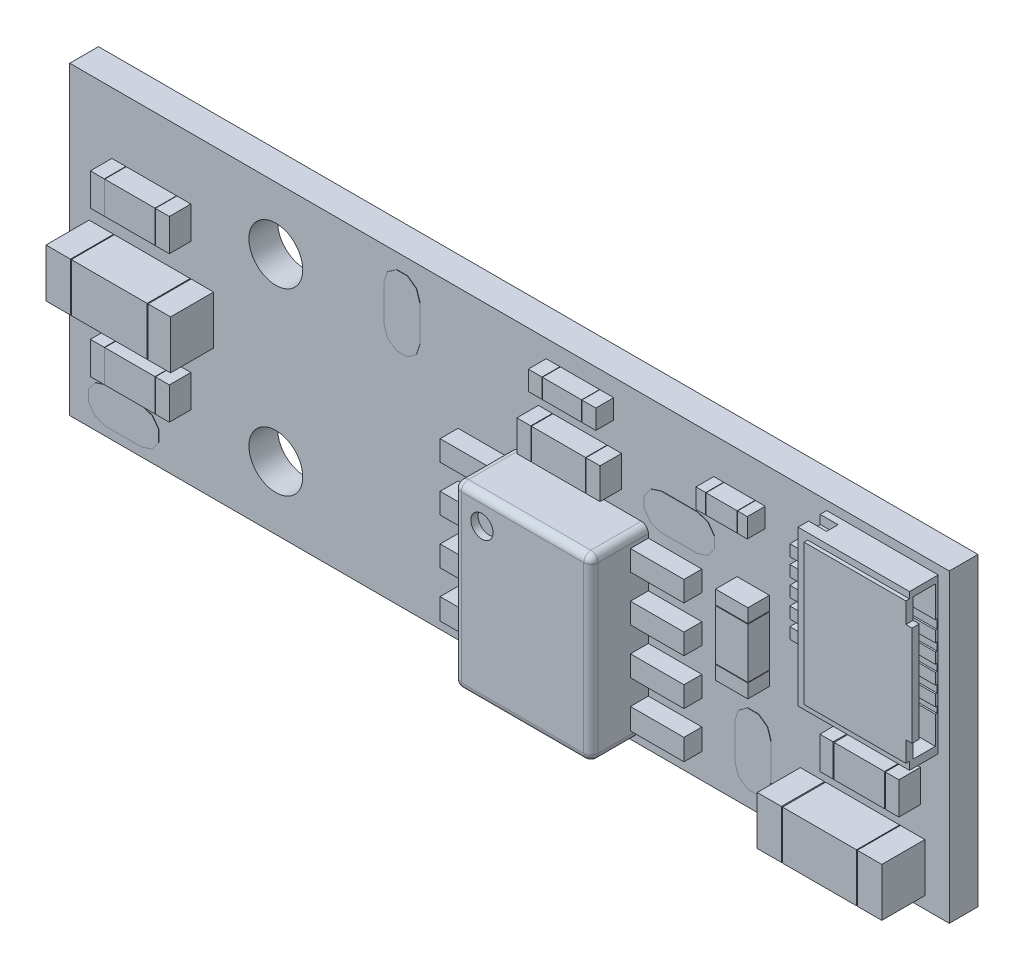
SolidWorks part; units mm, degrees
ref_plane "前视基准面" through (0, 0, 0) normal (0, 0, 1) x (1, 0, 0)
ref_plane "上视基准面" through (0, 0, 0) normal (0, 1, 0) x (1, 0, 0)
ref_plane "右视基准面" through (0, 0, 0) normal (1, 0, 0) x (0, 0, -1)
sketch "草图3" plane through (0, 0, 0) normal (0, 0, 1) x (1, 0, 0)
  line B0 (0, 8.5) -> (0, 0)
  line B1 (0.8695, 2.6826) -> (0.8695, 1.8826)
  line B2 (24.5, 8.5) -> (0, 8.5)
  line B3 (3.375, 5.891) -> (3.375, 6.791)
  line B4 (3.375, 6.791) -> (2.575, 6.791)
  line B5 (1.9793, 7.0564) -> (1.1793, 7.0564)
  line B6 (22.4108, 0.3313) -> (23.8205, 0.3313)
  line B7 (23.898, 0.1027) -> (22.4883, 0.1027)
  line B8 (0, 0) -> (24.5, 0)
  line B9 (22.4108, 1.6826) -> (22.4108, 0.3313)
  circle B10 centre (11.546, 5.452) radius 0.1499
  line B11 (9.1055, 6.1275) -> (8.8555, 6.3091)
  line B12 (21.7606, 1.6826) -> (20.3509, 1.6826)
  line B13 (21.0075, 6.2369) -> (20.3573, 6.2369)
  line B14 (20.3573, 5.9371) -> (21.0075, 5.9371)
  line B15 (19.489, 4.609) -> (19.489, 5.409)
  line B16 (18.589, 4.609) -> (19.489, 4.609)
  line B17 (17.8101, 3.7481) -> (17.8934, 3.547)
  line B18 (17.609, 3.8315) -> (17.8101, 3.7481)
  line B19 (16.2272, 3.8315) -> (17.609, 3.8315)
  line B20 (17.8101, 3.3458) -> (17.609, 3.2625)
  line B21 (17.8934, 3.547) -> (17.8101, 3.3458)
  arc B22 (18.3235, 3.2133) -> (18.6334, 2.9035) centre (18.6334, 3.2133) ccw
  line B23 (18.6345, 2.1819) -> (18.8845, 2.3635)
  line B24 (12.3999, 2.0758) -> (12.1988, 1.9925)
  line B25 (12.1988, 0.7225) -> (10.817, 0.7225)
  line B26 (12.1988, 1.9925) -> (10.817, 1.9925)
  line B27 (10.6158, 4.6158) -> (10.5325, 4.817)
  line B28 (12.1988, 4.5325) -> (10.817, 4.5325)
  line B29 (10.817, 3.8315) -> (12.1988, 3.8315)
  line B30 (10.817, 5.1015) -> (12.1988, 5.1015)
  line B31 (10.6158, 5.0182) -> (10.817, 5.1015)
  line B32 (3.665, 6.7408) -> (3.665, 5.9407)
  line B33 (2.575, 6.791) -> (2.575, 5.891)
  line B34 (1.9749, 5.891) -> (1.9749, 6.791)
  arc B35 (1.1793, 7.0564) -> (0.8694, 6.7466) centre (1.1793, 6.7466) ccw
  line B36 (1.9749, 6.791) -> (1.1749, 6.791)
  line B37 (2.575, 5.891) -> (3.375, 5.891)
  line B38 (2.5552, 5.631) -> (3.3552, 5.631)
  line B39 (2.6763, 5.2132) -> (4.086, 5.2132)
  line B40 (2.5988, 4.9846) -> (2.5988, 3.6334)
  line B41 (2.5552, 2.9866) -> (3.3552, 2.9866)
  line B42 (4.086, 3.4047) -> (2.6763, 3.4047)
  line B43 (1.9486, 3.6334) -> (1.9486, 4.9846)
  line B44 (1.9486, 4.9846) -> (0.5389, 4.9846)
  line B45 (2.5988, 3.6334) -> (4.0085, 3.6334)
  line B46 (2.5552, 1.567) -> (3.3552, 1.567)
  line B47 (1.9749, 1.827) -> (1.9749, 2.727)
  line B48 (1.9749, 2.727) -> (1.1749, 2.727)
  line B49 (2.575, 2.727) -> (2.575, 1.827)
  line B50 (2.575, 1.827) -> (3.375, 1.827)
  line B51 (17.8934, 4.817) -> (17.8101, 4.6158)
  line B52 (18.589, 5.409) -> (18.589, 4.609)
  circle B53 centre (19.039, 4.944) radius 0.305
  line B54 (20.3573, 5.2361) -> (20.3573, 4.9364)
  line B55 (20.3573, 5.4368) -> (21.0075, 5.4368)
  line B56 (19.749, 4.5893) -> (19.749, 5.3892)
  circle B57 centre (22.087, 6.3267) radius 0.305
  line B58 (20.3573, 6.9379) -> (21.0075, 6.9379)
  line B59 (19.6022, 7.7286) -> (19.6022, 6.7314)
  line B60 (19.3736, 6.96) -> (19.3736, 7.5)
  line B61 (18.808, 7.5) -> (18.808, 6.96)
  line B62 (18.508, 6.96) -> (18.508, 7.5)
  line B63 (17.9423, 6.96) -> (18.508, 6.96)
  line B64 (17.9423, 7.5) -> (17.9423, 6.96)
  line B65 (15.5973, 7.0014) -> (14.6397, 7.0014)
  line B66 (12.8287, 5.6806) -> (12.8287, 7.0014)
  line B67 (13.8625, 6.7728) -> (13.0547, 6.7728)
  line B68 (14.5635, 6.7728) -> (14.5635, 5.9092)
  line B69 (14.5635, 5.9092) -> (15.3712, 5.9092)
  line B70 (14.4392, 7.2394) -> (15.2293, 7.2394)
  line B71 (14.363, 7.468) -> (15.1531, 7.468)
  line B72 (14.363, 8.008) -> (14.363, 7.468)
  line B73 (14.0629, 7.468) -> (14.0629, 8.008)
  line B74 (14.0629, 8.008) -> (13.2728, 8.008)
  line B75 (15.3712, 6.7728) -> (14.5635, 6.7728)
  line B76 (16.0315, 5.8055) -> (16.0315, 6.1145)
  circle B77 centre (19.547, 6.214) radius 0.305
  line B78 (21.0075, 5.7365) -> (20.3573, 5.7365)
  line B79 (21.0075, 5.9371) -> (21.0075, 6.2369)
  line B80 (18.508, 7.5) -> (17.9423, 7.5)
  line B81 (18.808, 6.96) -> (19.3736, 6.96)
  line B82 (22.7918, 3.9369) -> (24.1914, 3.9369)
  line B83 (23.985, 3.3118) -> (23.985, 2.5117)
  line B84 (23.695, 2.462) -> (23.695, 3.362)
  line B85 (22.895, 2.462) -> (23.695, 2.462)
  line B86 (23.8205, 1.6826) -> (22.4108, 1.6826)
  line B87 (22.295, 2.462) -> (22.295, 3.362)
  line B88 (22.295, 3.362) -> (21.495, 3.362)
  line B89 (20.1236, 1.7588) -> (20.1236, 0.2551)
  line B90 (19.539, 1.888) -> (19.539, 0.888)
  line B91 (17.609, 1.9925) -> (16.2272, 1.9925)
  line B92 (17.609, 3.2625) -> (16.2272, 3.2625)
  line B93 (18.589, 3.209) -> (19.489, 3.209)
  line B94 (19.489, 3.209) -> (19.489, 4.009)
  arc B95 (19.749, 5.3892) -> (19.4392, 5.699) centre (19.4392, 5.3892) ccw
  line B96 (19.489, 5.409) -> (18.589, 5.409)
  line B97 (19.489, 4.009) -> (18.589, 4.009)
  line B98 (18.3294, 4.5893) -> (18.3294, 5.3892)
  line B99 (17.609, 4.5325) -> (16.2272, 4.5325)
  line B100 (20.3509, 0.3313) -> (21.7606, 0.3313)
  line B101 (20.276, 0.1027) -> (21.6857, 0.1027)
  line B102 (16.2272, 5.1015) -> (17.609, 5.1015)
  line B103 (15.5973, 5.6806) -> (15.5973, 7.0014)
  line B104 (13.1967, 8.2366) -> (13.9868, 8.2366)
  line B105 (17.7137, 6.7314) -> (18.4318, 6.7314)
  line B106 (20.3573, 6.2369) -> (20.3573, 5.9371)
  line B107 (23.9869, 7.5577) -> (23.9869, 4.6163)
  line B108 (24.3882, 7.8472) -> (24.3882, 4.3217)
  line B109 (17.7137, 7.7286) -> (17.7137, 6.7314)
  line B110 (15.3817, 7.3918) -> (15.3817, 8.0842)
  line B111 (19.6022, 6.7314) -> (18.8842, 6.7314)
  line B112 (18.4318, 7.7286) -> (17.7137, 7.7286)
  line B113 (12.1988, 3.8315) -> (12.3999, 3.7481)
  line B114 (18.3235, 4.0134) -> (18.3235, 3.2134)
  line B115 (21.7606, 0.3313) -> (21.7606, 1.6826)
  line B116 (17.609, 1.2915) -> (17.8101, 1.2081)
  circle B117 centre (14.213, 1.769) radius 0.305
  line B118 (4.2384, 5.0608) -> (4.2384, 3.5572)
  line B119 (0.3115, 5.0608) -> (0.3115, 3.5572)
  line B120 (3.665, 2.6768) -> (3.665, 1.8767)
  circle B121 centre (13.324, 1.007) radius 0.305
  line B122 (13.2728, 7.468) -> (14.0629, 7.468)
  line B123 (12.3999, 1.2081) -> (12.4832, 1.007)
  line B124 (15.7141, 0.4126) -> (12.7118, 0.4126)
  line B125 (12.7118, 0.4126) -> (12.308, 0.4126)
  line B126 (10.817, 1.2915) -> (12.1988, 1.2915)
  line B127 (12.1988, 3.2625) -> (10.817, 3.2625)
  line B128 (12.3999, 3.7481) -> (12.4832, 3.547)
  line B129 (4.0085, 4.9846) -> (2.5988, 4.9846)
  line B130 (8.8555, 6.3091) -> (8.76, 6.603)
  line B131 (12.3999, 2.4781) -> (12.4832, 2.277)
  line B132 (13.2728, 8.008) -> (13.2728, 7.468)
  line B133 (13.0547, 6.7728) -> (13.0547, 5.9092)
  line B134 (13.7863, 5.6806) -> (12.8287, 5.6806)
  line B135 (12.3999, 3.3458) -> (12.1988, 3.2625)
  line B136 (12.7118, 5.4114) -> (13.4865, 5.4114)
  circle B137 centre (3.291, 4.309) radius 0.305
  line B138 (1.1749, 5.891) -> (1.9749, 5.891)
  arc B139 (0.8694, 5.9466) -> (1.1793, 5.6368) centre (1.1793, 5.9466) ccw
  line B140 (1.8736, 5.2132) -> (0.4639, 5.2132)
  line B141 (3.375, 1.827) -> (3.375, 2.727)
  line B142 (1.1749, 1.827) -> (1.9749, 1.827)
  line B143 (1.1749, 2.727) -> (1.1749, 1.827)
  arc B144 (0.8694, 1.8826) -> (1.1793, 1.5728) centre (1.1793, 1.8826) ccw
  line B145 (10.6158, 1.2081) -> (10.817, 1.2915)
  line B146 (16.026, 3.3458) -> (15.9427, 3.547)
  line B147 (16.026, 3.7481) -> (16.2272, 3.8315)
  arc B148 (13.4864, 5.412) -> (14.9393, 5.4071) centre (14.213, 5.4518) ccw
  line B149 (14.6397, 5.6806) -> (15.5973, 5.6806)
  line B150 (15.3712, 5.9092) -> (15.3712, 6.7728)
  line B151 (12.7118, 5.4114) -> (12.308, 5.4114)
  line B152 (13.8625, 5.9092) -> (13.8625, 6.7728)
  line B153 (13.0547, 5.9092) -> (13.8625, 5.9092)
  line B154 (16.026, 4.6158) -> (15.9427, 4.817)
  line B155 (21.6857, 1.9112) -> (20.276, 1.9112)
  line B156 (22.8753, 2.202) -> (23.6752, 2.202)
  line B157 (21.495, 2.462) -> (22.295, 2.462)
  line B158 (22.895, 3.362) -> (22.895, 2.462)
  line B159 (16.507, 5.46) -> (16.2131, 5.5555)
  line B160 (18.6392, 5.699) -> (19.4392, 5.699)
  line B161 (17.9825, 5.8055) -> (17.8009, 5.5555)
  line B162 (16.026, 5.0182) -> (16.2272, 5.1015)
  line B163 (10.817, 3.8315) -> (12.1988, 3.8315)
  line B164 (16.2272, 1.2915) -> (17.609, 1.2915)
  line B165 (16.2272, 1.2915) -> (17.609, 1.2915)
  line B166 (17.609, 1.2915) -> (17.8101, 1.2081)
  line B167 (14.363, 7.468) -> (15.1531, 7.468)
  line B168 (13.0547, 6.7728) -> (13.0547, 5.9092)
  line B169 (1.1749, 5.891) -> (1.9749, 5.891)
  line B170 (15.9427, 2.277) -> (16.026, 2.4781)
  line B171 (0.5389, 3.6334) -> (1.9486, 3.6334)
  line B172 (0.5389, 4.9846) -> (0.5389, 3.6334)
  line B173 (0.4639, 3.4047) -> (1.8736, 3.4047)
  line B174 (1.9793, 2.9924) -> (1.1793, 2.9924)
  line B175 (16.2272, 2.5615) -> (17.609, 2.5615)
  line B176 (2.5552, 7.0506) -> (3.3552, 7.0506)
  line B177 (2.4885, 0.5985) -> (2.3068, 0.3485)
  line B178 (3.375, 2.727) -> (2.575, 2.727)
  line B179 (0.5374, 0.9075) -> (0.7191, 1.1575)
  line B180 (22.4883, 1.9112) -> (23.898, 1.9112)
  line B181 (23.695, 3.362) -> (22.895, 3.362)
  line B182 (17.507, 5.46) -> (16.507, 5.46)
  line B183 (12.8287, 7.0014) -> (13.7863, 7.0014)
  line B184 (12.4832, 4.817) -> (12.3999, 4.6158)
  line B185 (19.7432, 4.0134) -> (19.7432, 3.2134)
  line B186 (19.489, 3.209) -> (19.489, 4.009)
  line B187 (18.589, 4.609) -> (19.489, 4.609)
  line B188 (14.5635, 5.9092) -> (15.3712, 5.9092)
  line B189 (14.5635, 6.7728) -> (14.5635, 5.9092)
  line B190 (18.589, 4.009) -> (18.589, 3.209)
  line B191 (17.8101, 2.0758) -> (17.609, 1.9925)
  arc B192 (19.4334, 2.9035) -> (19.7432, 3.2133) centre (19.4334, 3.2133) ccw
  line B193 (18.6334, 2.9035) -> (19.4334, 2.9035)
  line B194 (10.817, 2.5615) -> (12.1988, 2.5615)
  line B195 (17.8009, 6.3645) -> (17.9825, 6.1145)
  line B196 (17.507, 6.46) -> (17.8009, 6.3645)
  line B197 (21.0075, 5.2361) -> (20.3573, 5.2361)
  line B198 (21.0075, 4.9364) -> (21.0075, 5.2361)
  line B199 (21.0862, 3.9229) -> (22.6128, 3.9229)
  line B200 (22.2994, 2.2078) -> (21.4994, 2.2078)
  line B201 (23.8205, 0.3313) -> (23.8205, 1.6826)
  line B202 (24.5, 0) -> (24.5, 8.5)
  line B203 (1.1749, 6.791) -> (1.1749, 5.891)
  line B204 (1.1749, 6.791) -> (1.1749, 5.891)
  arc B205 (21.1895, 2.5176) -> (21.4993, 2.2078) centre (21.4993, 2.5176) ccw
  line B206 (21.1895, 3.3176) -> (21.1895, 2.5176)
  arc B207 (21.4993, 3.6274) -> (21.1895, 3.3176) centre (21.4993, 3.3176) ccw
  line B208 (24.0504, 1.7588) -> (24.0504, 0.2551)
  line B209 (18.6345, 0.5941) -> (18.539, 0.888)
  line B210 (17.609, 2.5615) -> (17.8101, 2.4781)
  line B211 (21.495, 3.362) -> (21.495, 2.462)
  line B212 (15.2293, 8.2366) -> (14.4392, 8.2366)
  line B213 (15.1531, 7.468) -> (15.1531, 8.008)
  line B214 (15.1531, 8.008) -> (14.363, 8.008)
  line B215 (19.3736, 7.5) -> (18.808, 7.5)
  line B216 (10.6158, 2.0758) -> (10.5325, 2.277)
  line B217 (16.507, 5.46) -> (16.2131, 5.5555)
  line B218 (16.507, 6.46) -> (17.507, 6.46)
  line B219 (17.8934, 2.277) -> (17.8101, 2.0758)
  line B220 (18.539, 1.888) -> (18.6345, 2.1819)
  line B221 (17.8101, 2.4781) -> (17.8934, 2.277)
  line B222 (12.3999, 5.0182) -> (12.4832, 4.817)
  line B223 (12.1988, 5.1015) -> (12.3999, 5.0182)
  line B224 (9.6645, 6.3091) -> (9.4145, 6.1275)
  line B225 (9.76, 6.603) -> (9.6645, 6.3091)
  line B226 (9.76, 7.603) -> (9.76, 6.603)
  line B227 (10.5325, 4.817) -> (10.6158, 5.0182)
  line B228 (10.817, 4.5325) -> (10.6158, 4.6158)
  line B229 (16.026, 0.8058) -> (15.9427, 1.007)
  line B230 (16.2272, 0.7225) -> (16.026, 0.8058)
  line B231 (12.4832, 3.547) -> (12.3999, 3.3458)
  line B232 (10.5325, 1.007) -> (10.6158, 1.2081)
  line B233 (16.2272, 1.9925) -> (16.026, 2.0758)
  line B234 (12.3999, 4.6158) -> (12.1988, 4.5325)
  line B235 (12.3999, 0.8058) -> (12.1988, 0.7225)
  line B236 (18.539, 0.888) -> (18.539, 1.888)
  line B237 (16.026, 2.4781) -> (16.2272, 2.5615)
  line B238 (16.2272, 3.2625) -> (16.026, 3.3458)
  line B239 (17.609, 5.1015) -> (17.8101, 5.0182)
  line B240 (16.2272, 4.5325) -> (16.026, 4.6158)
  line B241 (13.9868, 7.2394) -> (13.1967, 7.2394)
  line B242 (17.609, 0.7225) -> (16.2272, 0.7225)
  line B243 (15.9427, 3.547) -> (16.026, 3.7481)
  line B244 (13.0443, 7.3918) -> (13.0443, 8.0842)
  line B245 (15.7141, 5.4114) -> (14.9394, 5.4114)
  line B246 (24.1914, 4.4373) -> (22.7918, 4.4373)
  line B247 (12.4832, 2.277) -> (12.3999, 2.0758)
  circle B248 centre (22.087, 7.23) radius 0.305
  line B249 (21.0862, 8.2511) -> (22.6128, 8.2511)
  line B250 (21.0862, 8.2511) -> (21.0862, 7.3976)
  line B251 (22.7918, 7.7367) -> (24.1914, 7.7367)
  line B252 (22.7918, 7.7367) -> (24.1914, 7.7367)
  line B253 (21.0075, 7.2376) -> (20.3573, 7.2376)
  line B254 (21.0075, 6.7372) -> (20.3573, 6.7372)
  line B255 (20.3573, 6.4375) -> (21.0075, 6.4375)
  line B256 (20.3573, 5.7365) -> (20.3573, 5.4368)
  line B257 (20.3573, 4.9364) -> (21.0075, 4.9364)
  line B258 (21.0862, 3.9229) -> (21.0862, 4.7764)
  line B259 (24.1914, 8.2371) -> (22.7918, 8.2371)
  line B260 (22.7918, 8.2371) -> (22.7918, 7.7367)
  arc B261 (18.6392, 5.699) -> (18.3294, 5.3892) centre (18.6392, 5.3892) ccw
  line B262 (17.8009, 5.5555) -> (17.507, 5.46)
  line B263 (19.489, 4.009) -> (18.589, 4.009)
  line B264 (19.4435, 2.1819) -> (19.539, 1.888)
  line B265 (19.4435, 2.1819) -> (19.539, 1.888)
  line B266 (22.4108, 1.6826) -> (22.4108, 0.3313)
  line B267 (22.4108, 0.3313) -> (23.8205, 0.3313)
  line B268 (20.3509, 1.6826) -> (20.3509, 0.3313)
  line B269 (20.3509, 1.6826) -> (20.3509, 0.3313)
  line B270 (21.0075, 7.2376) -> (20.3573, 7.2376)
  line B271 (20.3573, 6.4375) -> (21.0075, 6.4375)
  line B272 (22.7918, 8.2371) -> (22.7918, 7.7367)
  line B273 (21.0075, 6.2369) -> (20.3573, 6.2369)
  line B274 (21.0075, 4.9364) -> (21.0075, 5.2361)
  line B275 (20.3573, 5.9371) -> (21.0075, 5.9371)
  line B276 (19.1935, 2.3635) -> (19.4435, 2.1819)
  line B277 (19.1935, 2.3635) -> (19.4435, 2.1819)
  line B278 (21.0075, 5.2361) -> (20.3573, 5.2361)
  line B279 (21.7606, 1.6826) -> (20.3509, 1.6826)
  line B280 (20.3509, 0.3313) -> (21.7606, 0.3313)
  line B281 (10.6158, 3.3458) -> (10.5325, 3.547)
  line B282 (10.817, 3.2625) -> (10.6158, 3.3458)
  line B283 (0.7191, 1.1575) -> (1.013, 1.253)
  line B284 (2.3068, 1.1575) -> (2.4885, 0.9075)
  line B285 (2.4885, 0.9075) -> (2.4885, 0.5985)
  arc B286 (0.4638, 5.2126) -> (0.3114, 5.0602) centre (0.4638, 5.0602) ccw
  line B287 (8.76, 7.603) -> (8.8555, 7.8969)
  line B288 (2.013, 0.253) -> (1.013, 0.253)
  line B289 (8.76, 6.603) -> (8.76, 7.603)
  line B290 (9.6645, 7.8969) -> (9.76, 7.603)
  line B291 (9.4145, 8.0785) -> (9.6645, 7.8969)
  line B292 (9.1055, 8.0785) -> (9.4145, 8.0785)
  line B293 (8.8555, 7.8969) -> (9.1055, 8.0785)
  line B294 (9.4145, 6.1275) -> (9.1055, 6.1275)
  line B295 (1.9793, 1.5728) -> (1.1793, 1.5728)
  line B296 (2.013, 1.253) -> (2.3068, 1.1575)
  line B297 (0.5374, 0.5985) -> (0.5374, 0.9075)
  line B298 (0.7191, 0.3485) -> (0.5374, 0.5985)
  line B299 (1.013, 0.253) -> (0.7191, 0.3485)
  line B300 (2.3068, 0.3485) -> (2.013, 0.253)
  line B301 (1.013, 1.253) -> (2.013, 1.253)
  line B302 (10.5325, 2.277) -> (10.6158, 2.4781)
  line B303 (12.1988, 2.5615) -> (12.3999, 2.4781)
  arc B304 (1.1793, 2.9924) -> (0.8694, 2.6826) centre (1.1793, 2.6826) ccw
sketch_block_instance "DXF_PCB3_2023-05-06 (4)-1"
sketch_block "DXF_PCB3_2023-05-06 (4)"
sketch "草图4" plane through (0, 0, 0) normal (0, 0, 1) x (1, 0, 0)
  line L1 (24.5, 0) -> (0, 0)
  line L2 (24.5, 0) -> (24.5, 8.5)
  line L3 (24.5, 8.5) -> (0, 8.5)
  line L4 (0, 0) -> (0, 8.5)
extrude "凸台-拉伸1" add sketch "草图4" along normal blind 0.8
sketch "草图5" plane through (0, 0, 0.8) normal (0, 0, 1) x (1, 0, 0)
  line L0 (1.9749, 6.791) -> (1.1749, 6.791) construction
  line L1 (1.5749, 6.791) -> (2.975, 6.791)
  line L2 (1.5749, 6.791) -> (1.5749, 5.891)
  line L3 (1.5749, 5.891) -> (2.975, 5.891)
  line L4 (2.975, 6.791) -> (2.975, 5.891)
  line L5 (2.575, 5.891) -> (3.375, 5.891) construction
  line L12 (1.9749, 2.727) -> (1.1749, 2.727) construction
  line L13 (1.5749, 2.727) -> (2.975, 2.727)
  line L14 (1.5749, 2.727) -> (1.5749, 1.827)
  line L15 (1.5749, 1.827) -> (2.975, 1.827)
  line L16 (2.975, 2.727) -> (2.975, 1.827)
  line L17 (2.575, 1.827) -> (3.375, 1.827) construction
  line L18 (13.8625, 6.7728) -> (13.0547, 6.7728) construction
  line L19 (13.4586, 6.7728) -> (14.9674, 6.7728)
  line L20 (13.4586, 6.7728) -> (13.4586, 5.9092)
  line L21 (13.4586, 5.9092) -> (14.9674, 5.9092)
  line L22 (14.9674, 6.7728) -> (14.9674, 5.9092)
  line L23 (14.5635, 5.9092) -> (15.3712, 5.9092) construction
  line L36 (22.295, 3.362) -> (21.495, 3.362) construction
  line L37 (21.895, 3.362) -> (23.295, 3.362)
  line L38 (21.895, 3.362) -> (21.895, 2.462)
  line L39 (21.895, 2.462) -> (23.295, 2.462)
  line L40 (23.295, 3.362) -> (23.295, 2.462)
  line L41 (22.895, 2.462) -> (23.695, 2.462) construction
  line L48 (18.589, 5.409) -> (18.589, 4.609) construction
  line L49 (18.589, 5.009) -> (19.489, 5.009)
  line L50 (18.589, 5.009) -> (18.589, 3.609)
  line L51 (18.589, 3.609) -> (19.489, 3.609)
  line L52 (19.489, 5.009) -> (19.489, 3.609)
  line L53 (19.489, 3.209) -> (19.489, 4.009) construction
extrude "凸台-拉伸2" add sketch "草图5" along normal blind 0.6
sketch "草图7" plane through (0, 0, 0.8) normal (0, 0, 1) x (1, 0, 0)
  line L0 (3.375, 6.791) -> (2.575, 6.791) construction
  line L1 (3.375, 5.891) -> (2.9856, 5.891)
  line L2 (3.375, 5.891) -> (3.375, 6.791)
  line L3 (3.375, 6.791) -> (2.9856, 6.791)
  line L4 (2.9856, 5.891) -> (2.9856, 6.791)
  line L5 (1.1749, 5.891) -> (1.9749, 5.891) construction
  line L6 (1.1749, 6.791) -> (1.5619, 6.791)
  line L7 (1.1749, 6.791) -> (1.1749, 5.891)
  line L8 (1.1749, 5.891) -> (1.5619, 5.891)
  line L9 (1.5619, 6.791) -> (1.5619, 5.891)
  line L10 (2.575, 1.827) -> (3.375, 1.827) construction
  line L11 (3.375, 2.727) -> (2.9856, 2.727)
  line L12 (3.375, 2.727) -> (3.375, 1.827)
  line L13 (3.375, 1.827) -> (2.9856, 1.827)
  line L14 (2.9856, 2.727) -> (2.9856, 1.827)
  line L15 (1.1749, 1.827) -> (1.9749, 1.827) construction
  line L16 (1.1749, 2.727) -> (1.5619, 2.727)
  line L17 (1.1749, 2.727) -> (1.1749, 1.827)
  line L18 (1.1749, 1.827) -> (1.5619, 1.827)
  line L19 (1.5619, 2.727) -> (1.5619, 1.827)
  line L20 (23.695, 3.362) -> (22.895, 3.362) construction
  line L21 (23.695, 2.462) -> (23.3206, 2.462)
  line L22 (23.695, 2.462) -> (23.695, 3.362)
  line L23 (23.695, 3.362) -> (23.3206, 3.362)
  line L24 (23.3206, 2.462) -> (23.3206, 3.362)
  line L25 (21.495, 2.462) -> (22.295, 2.462) construction
  line L26 (21.495, 3.362) -> (21.8643, 3.362)
  line L27 (21.495, 3.362) -> (21.495, 2.462)
  line L28 (21.495, 2.462) -> (21.8643, 2.462)
  line L29 (21.8643, 3.362) -> (21.8643, 2.462)
  line L30 (13.0547, 5.9092) -> (13.8625, 5.9092) construction
  line L31 (13.0547, 6.7728) -> (13.4422, 6.7728)
  line L32 (13.0547, 6.7728) -> (13.0547, 5.9092)
  line L33 (13.0547, 5.9092) -> (13.4422, 5.9092)
  line L34 (13.4422, 6.7728) -> (13.4422, 5.9092)
  line L35 (14.5635, 5.9092) -> (15.3712, 5.9092) construction
  line L36 (15.3712, 6.7728) -> (14.979, 6.7728)
  line L37 (15.3712, 6.7728) -> (15.3712, 5.9092)
  line L38 (15.3712, 5.9092) -> (14.979, 5.9092)
  line L39 (14.979, 6.7728) -> (14.979, 5.9092)
  line L40 (19.489, 3.209) -> (19.489, 4.009) construction
  line L41 (18.589, 3.209) -> (19.489, 3.209)
  line L42 (18.589, 3.209) -> (18.589, 3.593)
  line L43 (18.589, 3.593) -> (19.489, 3.593)
  line L44 (19.489, 3.209) -> (19.489, 3.593)
  line L45 (19.489, 4.609) -> (19.489, 5.409) construction
  line L46 (18.589, 5.409) -> (19.489, 5.409)
  line L47 (18.589, 5.409) -> (18.589, 5.0285)
  line L48 (18.589, 5.0285) -> (19.489, 5.0285)
  line L49 (19.489, 5.409) -> (19.489, 5.0285)
extrude "凸台-拉伸4" add sketch "草图7" along normal blind 0.6
sketch "草图8" plane through (0, 0, 0.8) normal (0, 0, 1) x (1, 0, 0)
  line L0 (1.9486, 4.9846) -> (0.5389, 4.9846) construction
  line L1 (1.2437, 4.9846) -> (3.3552, 4.9846)
  line L2 (1.2437, 4.9846) -> (1.2437, 3.6334)
  line L3 (1.2437, 3.6334) -> (3.3552, 3.6334)
  line L4 (3.3552, 4.9846) -> (3.3552, 3.6334)
  line L5 (2.5988, 3.6334) -> (4.0085, 3.6334) construction
  line L6 (21.7606, 1.6826) -> (20.3509, 1.6826) construction
  line L7 (21.0558, 1.6826) -> (23.1157, 1.6826)
  line L8 (21.0558, 1.6826) -> (21.0558, 0.3313)
  line L9 (21.0558, 0.3313) -> (23.1157, 0.3313)
  line L10 (23.1157, 1.6826) -> (23.1157, 0.3313)
  line L11 (22.4108, 0.3313) -> (23.8205, 0.3313) construction
extrude "凸台-拉伸5" add sketch "草图8" along normal blind 1.2
sketch "草图9" plane through (0, 0, 0.8) normal (0, 0, 1) x (1, 0, 0)
  line L0 (0.5389, 3.6334) -> (1.9486, 3.6334) construction
  line L1 (0.5389, 4.9846) -> (1.221, 4.9846)
  line L2 (0.5389, 4.9846) -> (0.5389, 3.6334)
  line L3 (0.5389, 3.6334) -> (1.221, 3.6334)
  line L4 (1.221, 4.9846) -> (1.221, 3.6334)
  line L5 (2.5988, 3.6334) -> (4.0085, 3.6334) construction
  line L6 (4.0085, 4.9846) -> (3.382, 4.9846)
  line L7 (4.0085, 4.9846) -> (4.0085, 3.6334)
  line L8 (4.0085, 3.6334) -> (3.382, 3.6334)
  line L9 (3.382, 4.9846) -> (3.382, 3.6334)
  line L10 (20.3509, 0.3313) -> (21.7606, 0.3313) construction
  line L11 (20.3509, 1.6826) -> (21.0239, 1.6826)
  line L12 (20.3509, 1.6826) -> (20.3509, 0.3313)
  line L13 (20.3509, 0.3313) -> (21.0239, 0.3313)
  line L14 (21.0239, 1.6826) -> (21.0239, 0.3313)
  line L15 (22.4108, 0.3313) -> (23.8205, 0.3313) construction
  line L16 (23.8205, 1.6826) -> (23.1383, 1.6826)
  line L17 (23.8205, 1.6826) -> (23.8205, 0.3313)
  line L18 (23.8205, 0.3313) -> (23.1383, 0.3313)
  line L19 (23.1383, 1.6826) -> (23.1383, 0.3313)
extrude "凸台-拉伸6" add sketch "草图9" along normal blind 1.2
sketch "草图10" plane through (0, 0, 0.8) normal (0, 0, 1) x (1, 0, 0)
  line L0 (14.0629, 8.008) -> (13.2728, 8.008) construction
  line L1 (13.6679, 8.008) -> (14.7581, 8.008)
  line L2 (13.6679, 8.008) -> (13.6679, 7.468)
  line L3 (13.6679, 7.468) -> (14.7581, 7.468)
  line L4 (14.7581, 8.008) -> (14.7581, 7.468)
  line L5 (14.363, 7.468) -> (15.1531, 7.468) construction
  line L6 (18.508, 7.5) -> (17.9423, 7.5) construction
  line L7 (18.2252, 7.5) -> (19.0908, 7.5)
  line L8 (18.2252, 7.5) -> (18.2252, 6.96)
  line L9 (18.2252, 6.96) -> (19.0908, 6.96)
  line L10 (19.0908, 7.5) -> (19.0908, 6.96)
  line L11 (18.808, 6.96) -> (19.3736, 6.96) construction
extrude "凸台-拉伸7" add sketch "草图10" along normal blind 0.5
sketch "草图11" plane through (0, 0, 0.8) normal (0, 0, 1) x (1, 0, 0)
  line L0 (13.2728, 7.468) -> (14.0629, 7.468) construction
  line L1 (13.2728, 8.008) -> (13.6561, 8.008)
  line L2 (13.2728, 8.008) -> (13.2728, 7.468)
  line L3 (13.2728, 7.468) -> (13.6561, 7.468)
  line L4 (13.6561, 8.008) -> (13.6561, 7.468)
  line L5 (14.363, 7.468) -> (15.1531, 7.468) construction
  line L6 (15.1531, 8.008) -> (14.7661, 8.008)
  line L7 (15.1531, 8.008) -> (15.1531, 7.468)
  line L8 (15.1531, 7.468) -> (14.7661, 7.468)
  line L9 (14.7661, 8.008) -> (14.7661, 7.468)
  line L10 (17.9423, 6.96) -> (18.508, 6.96) construction
  line L11 (17.9423, 7.5) -> (18.214, 7.5)
  line L12 (17.9423, 7.5) -> (17.9423, 6.96)
  line L13 (17.9423, 6.96) -> (18.214, 6.96)
  line L14 (18.214, 7.5) -> (18.214, 6.96)
  line L15 (18.808, 6.96) -> (19.3736, 6.96) construction
  line L16 (19.3736, 7.5) -> (19.1014, 7.5)
  line L17 (19.3736, 7.5) -> (19.3736, 6.96)
  line L18 (19.3736, 6.96) -> (19.1014, 6.96)
  line L19 (19.1014, 7.5) -> (19.1014, 6.96)
extrude "凸台-拉伸8" add sketch "草图11" along normal blind 0.5
sketch "草图12" plane through (0, 0, 0.8) normal (0, 0, 1) x (1, 0, 0)
  line L1 (12.308, 5.4114) -> (16.118, 5.4114)
  line L2 (12.308, 5.4114) -> (12.308, 0.4126)
  line L3 (12.308, 0.4126) -> (16.118, 0.4126)
  line L4 (16.118, 5.4114) -> (16.118, 0.4126)
extrude "凸台-拉伸9" add sketch "草图12" along normal blind 1.6
sketch "草图13" plane through (0, 0, 0.8) normal (0, 0, 1) x (1, 0, 0)
  line L0 (12.308, 5.4114) -> (12.308, 0.4126) construction
  line L1 (10.817, 5.1015) -> (12.308, 5.1015)
  line L2 (10.817, 5.1015) -> (10.817, 4.5336)
  line L3 (10.817, 4.5336) -> (12.308, 4.5336)
  line L4 (12.308, 5.1015) -> (12.308, 4.5336)
  line L5 (16.118, 0.4126) -> (16.118, 5.4114) construction
  line L6 (10.817, 3.8315) -> (12.308, 3.8315)
  line L7 (10.817, 3.8315) -> (10.817, 3.2596)
  line L8 (10.817, 3.2596) -> (12.308, 3.2596)
  line L9 (12.308, 3.8315) -> (12.308, 3.2596)
  line L10 (10.817, 2.5615) -> (12.308, 2.5615)
  line L11 (10.817, 2.5615) -> (10.817, 1.9853)
  line L12 (10.817, 1.9853) -> (12.308, 1.9853)
  line L13 (12.308, 2.5615) -> (12.308, 1.9853)
  line L14 (10.817, 1.2915) -> (12.308, 1.2915)
  line L15 (10.817, 1.2915) -> (10.817, 0.7015)
  line L16 (10.817, 0.7015) -> (12.308, 0.7015)
  line L17 (12.308, 1.2915) -> (12.308, 0.7015)
  line L18 (17.609, 1.2915) -> (16.118, 1.2915)
  line L19 (17.609, 1.2915) -> (17.609, 0.7015)
  line L20 (17.609, 0.7015) -> (16.118, 0.7015)
  line L21 (16.118, 1.2915) -> (16.118, 0.7015)
  line L22 (16.118, 0.4126) -> (16.118, 5.4114) construction
  line L23 (17.609, 2.5615) -> (16.118, 2.5615)
  line L24 (17.609, 2.5615) -> (17.609, 1.9853)
  line L25 (17.609, 1.9853) -> (16.118, 1.9853)
  line L26 (16.118, 2.5615) -> (16.118, 1.9853)
  line L27 (17.609, 3.8315) -> (16.118, 3.8315)
  line L28 (17.609, 3.8315) -> (17.609, 3.2596)
  line L29 (17.609, 3.2596) -> (16.118, 3.2596)
  line L30 (16.118, 3.8315) -> (16.118, 3.2596)
  line L32 (17.609, 5.1015) -> (16.118, 5.1015)
  line L33 (17.609, 5.1015) -> (17.609, 4.5336)
  line L34 (17.609, 4.5336) -> (16.118, 4.5336)
  line L35 (16.118, 5.1015) -> (16.118, 4.5336)
extrude "凸台-拉伸10" add sketch "草图13" along normal blind 0.5
sketch "草图14" plane through (0, 0, 2.4) normal (0, 0, 1) x (1, 0, 0)
  circle A0 centre (13.0829, 4.6684) radius 0.3094
extrude "切除-拉伸1" cut sketch "草图14" against normal blind 0.2
sketch "草图15" plane through (0, 0, 0.8) normal (0, 0, 1) x (1, 0, 0)
  line L1 (21.0862, 8.2511) -> (24.1914, 8.2511)
  line L2 (21.0862, 8.2511) -> (21.0862, 3.9369)
  line L3 (21.0862, 3.9369) -> (24.1914, 3.9369)
  line L4 (24.1914, 8.2511) -> (24.1914, 3.9369)
extrude "凸台-拉伸11" add sketch "草图15" along normal blind 0.8
sketch "草图16" plane through (0, 0, 0.8) normal (0, 0, 1) x (1, 0, 0)
  line L0 (21.0862, 8.2511) -> (21.0862, 3.9369) construction
  line L1 (20.3573, 7.2376) -> (21.0862, 7.2376)
  line L2 (20.3573, 7.2376) -> (20.3573, 6.925)
  line L3 (20.3573, 6.925) -> (21.0862, 6.925)
  line L4 (21.0862, 7.2376) -> (21.0862, 6.925)
  line L5 (21.0862, 8.2511) -> (21.0862, 3.9369) construction
  line L6 (20.3573, 6.7372) -> (21.0862, 6.7372)
  line L7 (20.3573, 6.7372) -> (20.3573, 6.4357)
  line L8 (20.3573, 6.4357) -> (21.0862, 6.4357)
  line L9 (21.0862, 6.7372) -> (21.0862, 6.4357)
  line L11 (20.3573, 6.2369) -> (21.0862, 6.2369)
  line L12 (20.3573, 6.2369) -> (20.3573, 5.9402)
  line L13 (20.3573, 5.9402) -> (21.0862, 5.9402)
  line L14 (21.0862, 6.2369) -> (21.0862, 5.9402)
  line L15 (20.3573, 5.7365) -> (21.0862, 5.7365)
  line L16 (20.3573, 5.7365) -> (20.3573, 5.4215)
  line L17 (20.3573, 5.4215) -> (21.0862, 5.4215)
  line L18 (21.0862, 5.7365) -> (21.0862, 5.4215)
  line L19 (20.3573, 5.2361) -> (21.0862, 5.2361)
  line L20 (20.3573, 5.2361) -> (20.3573, 4.9321)
  line L21 (20.3573, 4.9321) -> (21.0862, 4.9321)
  line L22 (21.0862, 5.2361) -> (21.0862, 4.9321)
extrude "凸台-拉伸12" add sketch "草图16" along normal blind 0.3
sketch "草图17" plane through (21.0862, 0, 0) normal (-1, 0, 0) x (0, 0, 1)
  line L0 (1.6, 3.9369) -> (0.8, 3.9369) construction
  line L1 (1.3044, 3.9369) -> (0.983, 3.9369)
  line L2 (1.3044, 3.9369) -> (1.3044, 4.1865)
  line L3 (1.3044, 4.1865) -> (0.983, 4.1865)
  line L4 (0.983, 3.9369) -> (0.983, 4.1865)
  line L5 (1.6, 8.2511) -> (0.8, 8.2511) construction
  line L6 (1.3044, 8.2511) -> (0.983, 8.2511)
  line L7 (1.3044, 8.2511) -> (1.3044, 8.0062)
  line L8 (1.3044, 8.0062) -> (0.983, 8.0062)
  line L9 (0.983, 8.2511) -> (0.983, 8.0062)
extrude "切除-拉伸2" cut sketch "草图17" against normal blind 0.5
sketch "草图18" plane through (24.1914, 0, 0) normal (1, 0, 0) x (0, 0, -1)
  line L1 (-0.8806, 4.157) -> (-1.7626, 4.157)
  line L2 (-0.8806, 4.157) -> (-0.8806, 8.0741)
  line L3 (-0.8806, 8.0741) -> (-1.7626, 8.0741)
  line L4 (-1.7626, 4.157) -> (-1.7626, 8.0741)
extrude "切除-拉伸3" cut sketch "草图18" against normal blind 2.5
sketch "草图19" plane through (24.1914, 0, 0) normal (1, 0, 0) x (0, 0, -1)
  line L0 (-1.1, 4.9321) -> (-0.8, 4.9321) construction
  line L1 (-0.8357, 4.9321) -> (-1.4634, 4.9321)
  line L2 (-0.8357, 4.9321) -> (-0.8357, 5.1078)
  line L3 (-0.8357, 5.1078) -> (-1.4634, 5.1078)
  line L4 (-1.4634, 4.9321) -> (-1.4634, 5.1078)
  line L5 (-1.1, 5.4215) -> (-0.8, 5.4215) construction
  line L6 (-0.8357, 5.4215) -> (-1.4634, 5.4215)
  line L7 (-0.8357, 5.4215) -> (-0.8357, 5.6332)
  line L8 (-0.8357, 5.6332) -> (-1.4634, 5.6332)
  line L9 (-1.4634, 5.4215) -> (-1.4634, 5.6332)
  line L10 (-1.1, 5.9402) -> (-0.8, 5.9402) construction
  line L11 (-0.8357, 5.9402) -> (-1.4634, 5.9402)
  line L12 (-0.8357, 5.9402) -> (-0.8357, 6.1358)
  line L13 (-0.8357, 6.1358) -> (-1.4634, 6.1358)
  line L14 (-1.4634, 5.9402) -> (-1.4634, 6.1358)
  line L15 (-1.1, 6.4357) -> (-0.8, 6.4357) construction
  line L16 (-0.8357, 6.4357) -> (-1.4634, 6.4357)
  line L17 (-0.8357, 6.4357) -> (-0.8357, 6.6527)
  line L18 (-0.8357, 6.6527) -> (-1.4634, 6.6527)
  line L19 (-1.4634, 6.4357) -> (-1.4634, 6.6527)
  line L20 (-1.3, 6.96) -> (-0.8, 6.96) construction
  line L21 (-0.8357, 6.96) -> (-1.4634, 6.96)
  line L22 (-0.8357, 6.96) -> (-0.8357, 7.2094)
  line L23 (-0.8357, 7.2094) -> (-1.4634, 7.2094)
  line L24 (-1.4634, 6.96) -> (-1.4634, 7.2094)
extrude "切除-拉伸4" cut sketch "草图19" against normal blind 2.8
sketch "草图20" plane through (0, 0, 1.6) normal (0, 0, 1) x (1, 0, 0)
  line L0 (24.1914, 4.157) -> (24.1914, 4.7241)
  line L1 (24.1914, 4.157) -> (24.1914, 4.9321) construction
  line L2 (24.1914, 4.7241) -> (24.3624, 4.7241)
  line L3 (24.3624, 4.7241) -> (24.3624, 7.5046)
  line L4 (24.3624, 7.5046) -> (24.1914, 7.5046)
  line L5 (24.1914, 7.2094) -> (24.1914, 8.0741) construction
  line L6 (24.1914, 7.5046) -> (24.1914, 8.0741)
  line L7 (24.1914, 8.0741) -> (21.3557, 8.0741)
  line L8 (21.3557, 8.0741) -> (21.3557, 4.157)
  line L9 (21.3557, 4.157) -> (24.1914, 4.157)
extrude "凸台-拉伸13" add sketch "草图20" along normal mid plane 0.2
sketch "草图21" plane through (0, 0, 0.8) normal (0, 0, 1) x (1, 0, 0)
  line L0 (19.4443, 0.6255) -> (19.5398, 0.9194)
  line L1 (19.1943, 0.4438) -> (19.4443, 0.6255)
  line L2 (18.8853, 0.4438) -> (19.1943, 0.4438)
  line L3 (18.6353, 0.6255) -> (18.8853, 0.4438)
  line L4 (18.5398, 0.9194) -> (18.6353, 0.6255)
  line L5 (18.5398, 1.9194) -> (18.5398, 0.9194)
  line L6 (18.6353, 2.2133) -> (18.5398, 1.9194)
  line L7 (18.8853, 2.3949) -> (18.6353, 2.2133)
  line L8 (19.1943, 2.3949) -> (18.8853, 2.3949)
  line L9 (19.4443, 2.2133) -> (19.1943, 2.3949)
  line L10 (19.5398, 1.9194) -> (19.4443, 2.2133)
  line L11 (19.5398, 0.9194) -> (19.5398, 1.9194)
  line L12 (16.4888, 6.4249) -> (16.1949, 6.3294)
  line L13 (17.4888, 6.4249) -> (16.4888, 6.4249)
  line L14 (17.7827, 6.3294) -> (17.4888, 6.4249)
  line L15 (17.9643, 6.0794) -> (17.7827, 6.3294)
  line L16 (17.9643, 5.7704) -> (17.9643, 6.0794)
  line L17 (17.7827, 5.5204) -> (17.9643, 5.7704)
  line L18 (17.4888, 5.4249) -> (17.7827, 5.5204)
  line L19 (16.4888, 5.4249) -> (17.4888, 5.4249)
  line L20 (16.1949, 5.5204) -> (16.4888, 5.4249)
  line L21 (16.0132, 5.7704) -> (16.1949, 5.5204)
  line L22 (16.0132, 6.0794) -> (16.0132, 5.7704)
  line L23 (16.1949, 6.3294) -> (16.0132, 6.0794)
  line L94 (9.6645, 6.3091) -> (9.76, 6.603)
  line L95 (9.4145, 6.1275) -> (9.6645, 6.3091)
  line L96 (9.1055, 6.1275) -> (9.4145, 6.1275)
  line L97 (8.8555, 6.3091) -> (9.1055, 6.1275)
  line L98 (8.76, 6.603) -> (8.8555, 6.3091)
  line L99 (8.76, 7.603) -> (8.76, 6.603)
  line L100 (8.8555, 7.8969) -> (8.76, 7.603)
  line L101 (9.1055, 8.0785) -> (8.8555, 7.8969)
  line L102 (9.4145, 8.0785) -> (9.1055, 8.0785)
  line L103 (9.6645, 7.8969) -> (9.4145, 8.0785)
  line L104 (9.76, 7.603) -> (9.6645, 7.8969)
  line L105 (9.76, 6.603) -> (9.76, 7.603)
  line L106 (9.6645, 6.3091) -> (9.76, 6.603)
  line L107 (9.4145, 6.1275) -> (9.6645, 6.3091)
  line L108 (9.1055, 6.1275) -> (9.4145, 6.1275)
  line L109 (8.8555, 6.3091) -> (9.1055, 6.1275)
  line L110 (8.76, 6.603) -> (8.8555, 6.3091)
  line L111 (8.76, 7.603) -> (8.76, 6.603)
  line L112 (8.8555, 7.8969) -> (8.76, 7.603)
  line L113 (9.1055, 8.0785) -> (8.8555, 7.8969)
  line L114 (9.4145, 8.0785) -> (9.1055, 8.0785)
  line L115 (9.6645, 7.8969) -> (9.4145, 8.0785)
  line L116 (9.76, 7.603) -> (9.6645, 7.8969)
  line L117 (9.76, 6.603) -> (9.76, 7.603)
  line L126 (1.013, 1.253) -> (0.7191, 1.1575)
  line L127 (2.013, 1.253) -> (1.013, 1.253)
  line L128 (2.3068, 1.1575) -> (2.013, 1.253)
  line L129 (2.4885, 0.9075) -> (2.3068, 1.1575)
  line L130 (2.4885, 0.5985) -> (2.4885, 0.9075)
  line L131 (2.3068, 0.3485) -> (2.4885, 0.5985)
  line L132 (2.013, 0.253) -> (2.3068, 0.3485)
  line L133 (1.013, 0.253) -> (2.013, 0.253)
  line L134 (0.7191, 0.3485) -> (1.013, 0.253)
  line L135 (0.5374, 0.5985) -> (0.7191, 0.3485)
  line L136 (0.5374, 0.9075) -> (0.5374, 0.5985)
  line L137 (0.7191, 1.1575) -> (0.5374, 0.9075)
  line L138 (1.013, 1.253) -> (0.7191, 1.1575)
  line L139 (2.013, 1.253) -> (1.013, 1.253)
  line L140 (2.3068, 1.1575) -> (2.013, 1.253)
  line L141 (2.4885, 0.9075) -> (2.3068, 1.1575)
  line L142 (2.4885, 0.5985) -> (2.4885, 0.9075)
  line L143 (2.3068, 0.3485) -> (2.4885, 0.5985)
  line L144 (2.013, 0.253) -> (2.3068, 0.3485)
  line L145 (1.013, 0.253) -> (2.013, 0.253)
  line L146 (0.7191, 0.3485) -> (1.013, 0.253)
  line L147 (0.5374, 0.5985) -> (0.7191, 0.3485)
  line L148 (0.5374, 0.9075) -> (0.5374, 0.5985)
  line L149 (0.7191, 1.1575) -> (0.5374, 0.9075)
  dimension "D1" = 0
  dimension "D2" = 0
extrude "凸台-拉伸14" add sketch "草图21" along normal blind 0.01
fillet "圆角1" radius 0.2 8 edges at (16.118, 5.4114, 1.6) (14.213, 5.4114, 2.4) (16.118, 2.912, 2.4) (14.213, 0.4126, 2.4) (16.118, 0.4126, 1.6) (12.308, 0.4126, 1.6) (12.308, 2.912, 2.4) (12.308, 5.4114, 1.6)
ref_plane "基准面1" through (2.9856, 5.891, 0.8) normal (1, 0, 0) x (0, 0, -1)
sketch "草图23" plane through (0, 0, 0.8) normal (0, 0, 1) x (1, 0, 0)
sketch_block_instance "DXF_PCB3_2023-05-06 (6)-1"
sketch_block "DXF_PCB3_2023-05-06 (6)"
sketch "草图24" plane through (0, 0, 0.8) normal (0, 0, 1) x (1, 0, 0)
  circle A0 centre (5.741, 6.763) radius 0.75
  circle A1 centre (5.741, 1.763) radius 0.75
  dimension "D1" = 1.5
extrude "切除-拉伸5" cut sketch "草图24" against normal through all
